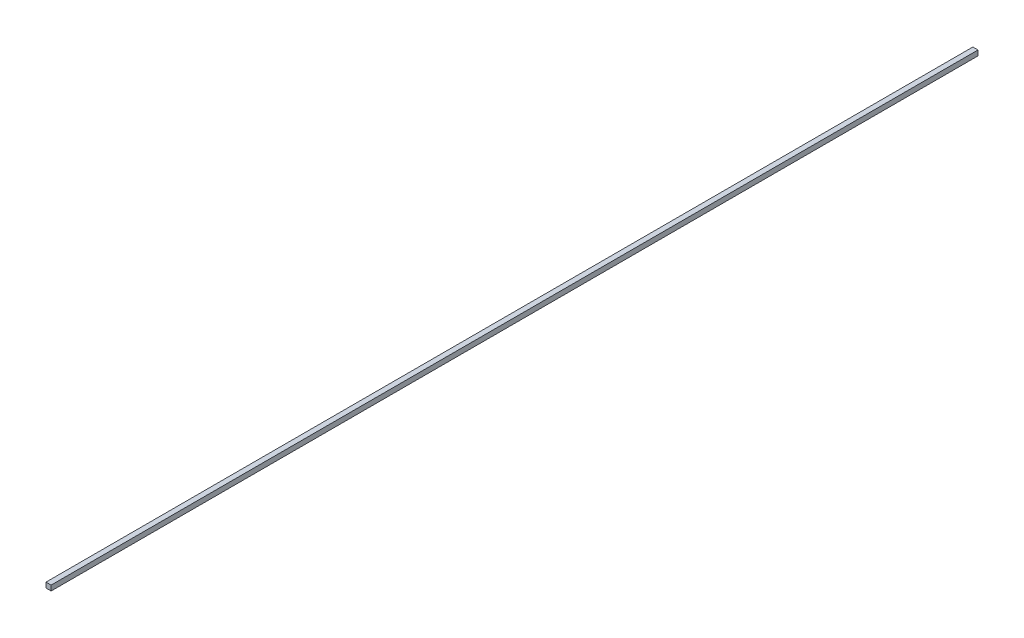
SolidWorks part; units mm, degrees
ref_plane "Front Plane" through (0, 0, 0) normal (0, 0, 1) x (1, 0, 0)
ref_plane "Top Plane" through (0, 0, 0) normal (0, 1, 0) x (1, 0, 0)
ref_plane "Right Plane" through (0, 0, 0) normal (1, 0, 0) x (0, 0, -1)
sketch "Sketch1" plane through (0, 0, 0) normal (0, 0, 1) x (1, 0, 0)
  line L1 (-5, 5) -> (5, 5)
  line L2 (-5, 5) -> (-5, -5)
  line L3 (-5, -5) -> (5, -5)
  line L4 (5, 5) -> (5, -5)
  line L5 (-5, 5) -> (5, -5) construction
  line L6 (-5, -5) -> (5, 5) construction
  point P0 (0, 0)
  dimension "D1" = 10
  dimension "D2" = 10
extrude "Boss-Extrude1" add sketch "Sketch1" along normal blind 1800
